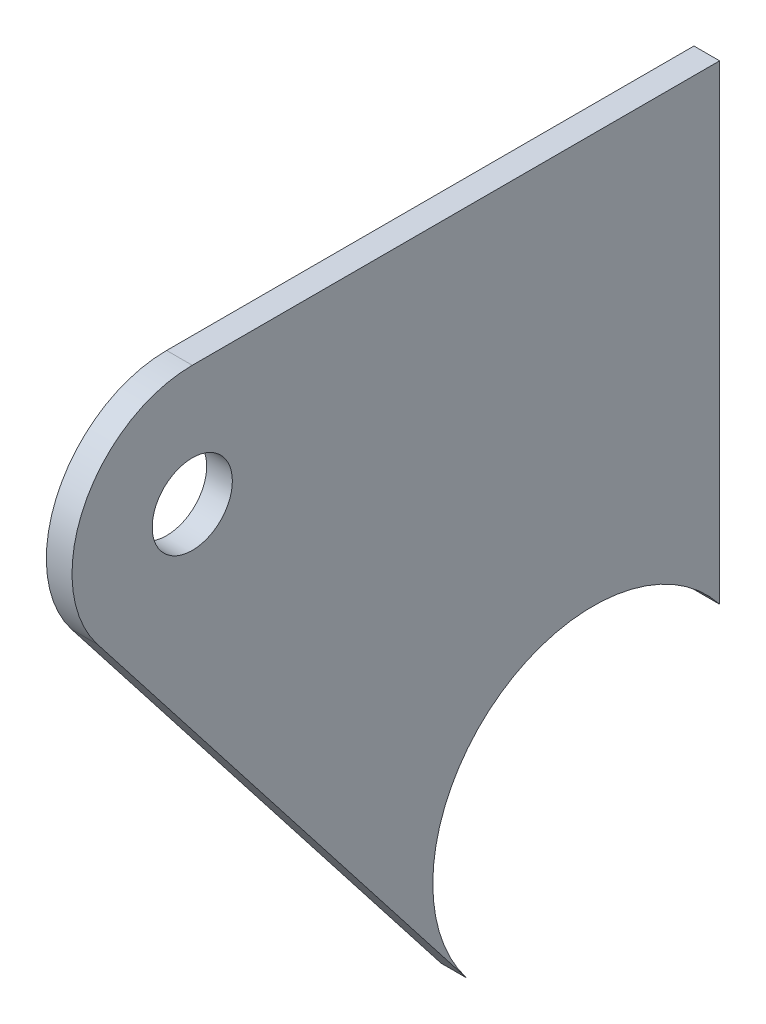
SolidWorks part; units mm, degrees
material "Plain Carbon Steel"
ref_plane "Front Plane" through (0, 0, 0) normal (0, 0, 1) x (1, 0, 0)
ref_plane "Top Plane" through (0, 0, 0) normal (0, 1, 0) x (1, 0, 0)
ref_plane "Right Plane" through (0, 0, 0) normal (1, 0, 0) x (0, 0, -1)
sketch "Sketch1" plane through (0, 0, 0) normal (1, 0, 0) x (0, 0, -1)
  line L9 (-10.0157, -7.8087) -> (-39.2618, 29.7035)
  line L10 (-31.75, 45.085) -> (10.0157, 45.085)
  line L11 (10.0157, 45.085) -> (10.0157, 7.8087)
  line L12 (-10.0157, -7.8087) -> (10.0157, 7.8087) construction
  arc A0 (10.0157, 7.8087) -> (-10.0157, -7.8087) centre (0, 0) ccw
  circle A1 centre (-31.75, 35.56) radius 3.175
  arc A2 (-39.2618, 29.7035) -> (-31.75, 45.085) centre (-31.75, 35.56) cw
  point P1 (0, 0)
  dimension "D1" = 25.4
  dimension "D2" = 6.35
  dimension "D5" = 6.35
  dimension "D3" = 31.75
  dimension "D4" = 35.56
extrude "Boss-Extrude1" add sketch "Sketch1" along direction (1, 0, 0) on the side of the normal blind 2.032 from offset 12.7
